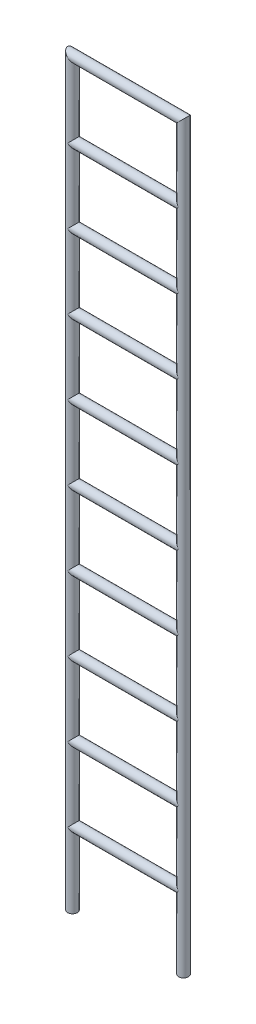
SolidWorks part; units mm, degrees
ref_plane "Front Plane" through (0, 0, 0) normal (0, 0, 1) x (1, 0, 0)
ref_plane "Top Plane" through (0, 0, 0) normal (0, 1, 0) x (1, 0, 0)
ref_plane "Right Plane" through (0, 0, 0) normal (1, 0, 0) x (0, 0, -1)
sketch "Sketch2" plane through (0, 0, 0) normal (0, 0, 1) x (1, 0, 0)
  line L0 (0, -92.3755) -> (0, -3140.3755)
  line L1 (-457.2, -92.3755) -> (-457.2, -3140.3755)
  line L2 (-457.2, -397.1755) -> (0, -397.1755)
  line L3 (-457.2, -1616.3755) -> (0, -1616.3755)
  line L4 (-457.2, -2530.7755) -> (0, -2530.7755)
  line L5 (-457.2, -701.9755) -> (0, -701.9755)
  line L6 (-457.2, -2225.9755) -> (0, -2225.9755)
  line L7 (-457.2, -1006.7755) -> (0, -1006.7755)
  line L8 (-457.2, -1311.5755) -> (0, -1311.5755)
  line L9 (-457.2, -1921.1755) -> (0, -1921.1755)
  line L10 (-457.2, -92.3755) -> (0, -92.3755)
  line L11 (-457.2, -2835.5755) -> (0, -2835.5755)
  point P26 (-228.6, -1616.3755)
  dimension "D1" = 3048
  dimension "D2" = 457.2
  dimension "D3" = 304.8
  dimension "D4" = 304.8
  dimension "D5" = 304.8
  dimension "D6" = 304.8
  dimension "D7" = 304.8
  dimension "D8" = 304.8
  dimension "D9" = 304.8
  dimension "D10" = 304.8
  dimension "D11" = 3048
sketch "Sketch3" plane through (0, 0, 0) normal (0, 0, 1) x (1, 0, 0)
  line L0 (0, 0) -> (0, 304.8)
  line L1 (0, 304.8) -> (457.2, 304.8)
  line L2 (457.2, 304.8) -> (457.2, 0)
  dimension "D1" = 457.2
  dimension "D2" = 304.8
sweep "Sweep1" add path "Sketch3" circular profile diameter 40 parameters "D3"=40
pattern_linear "LPattern1" count 10 spacing 304.8 along (0, 1, 0) of "Sweep1"
sketch "Sketch4" plane through (0, 0, 0) normal (0, 0, 1) x (1, 0, 0)
  line L0 (0, 0) -> (0, 165.8787) construction
  line L1 (0, 0) -> (327.3409, 0) construction
